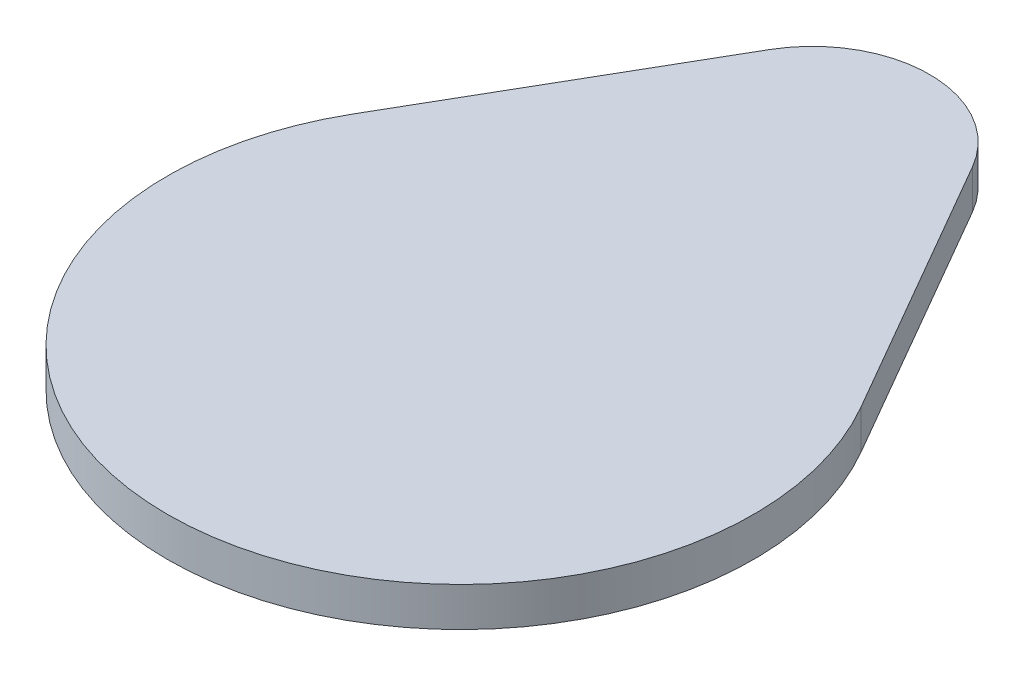
SolidWorks part; units mm, degrees
ref_plane "Front Plane" through (0, 0, 0) normal (0, 0, 1) x (1, 0, 0)
ref_plane "Top Plane" through (0, 0, 0) normal (0, 1, 0) x (1, 0, 0)
ref_plane "Right Plane" through (0, 0, 0) normal (1, 0, 0) x (0, 0, -1)
sketch "Sketch1" plane through (0, 0, 0) normal (0, 1, 0) x (1, 0, 0)
  line L0 (0, 23.9744) -> (0, -21.2354) construction
  line L1 (0, 15) -> (-6.4952, 3.75)
  line L2 (0, 15) -> (6.4952, 3.75)
  circle A0 centre (0, 0) radius 7.5
  dimension "D1" = 15
  dimension "D2" = 15
extrude "Boss-Extrude1" add sketch "Sketch1" along normal blind 1 contours L2 L0 A0 | L0 L1 A0 | A0 L0 | L0 A0
fillet "Fillet1" radius 3 1 edges at (0, 0.5, -15)
